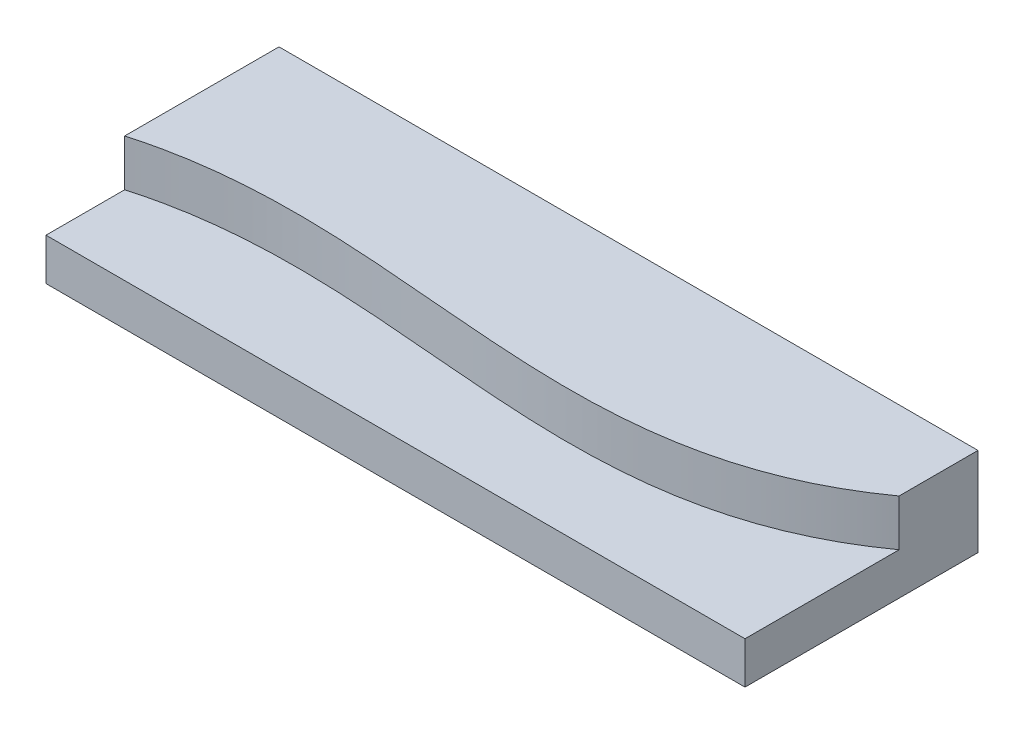
SolidWorks part; units mm, degrees
ref_plane "Front Plane" through (0, 0, 0) normal (0, 0, 1) x (1, 0, 0)
ref_plane "Top Plane" through (0, 0, 0) normal (0, 1, 0) x (1, 0, 0)
ref_plane "Right Plane" through (0, 0, 0) normal (1, 0, 0) x (0, 0, -1)
sketch "Sketch1" plane through (0, 0, 0) normal (0, 1, 0) x (1, 0, 0)
  line L1 (0, 0) -> (150, 0)
  line L2 (0, 0) -> (0, 50)
  line L3 (0, 50) -> (150, 50)
  line L4 (150, 0) -> (150, 50)
  dimension "D1" = 50
  dimension "D2" = 150
extrude "Boss-Extrude1" add sketch "Sketch1" along normal blind 19
sketch "Sketch2" plane through (0, 19, 0) normal (0, 1, 0) x (1, 0, 0)
  line L0 (-14.1577, 11.436) -> (-14.1577, -14.1056)
  line L1 (-14.1577, -14.1056) -> (161.6194, -14.1056)
  line L2 (161.6194, -14.1056) -> (161.6194, 43.1647)
  spline S0 degree 3 poles (-14.1577, 11.436) (43.4068, 39.6999) (110.7504, -9.2894) (161.6194, 43.1647) knots 0 0 0 0 1 1 1 1
extrude "Cut-Extrude1" cut sketch "Sketch2" against normal blind 10
